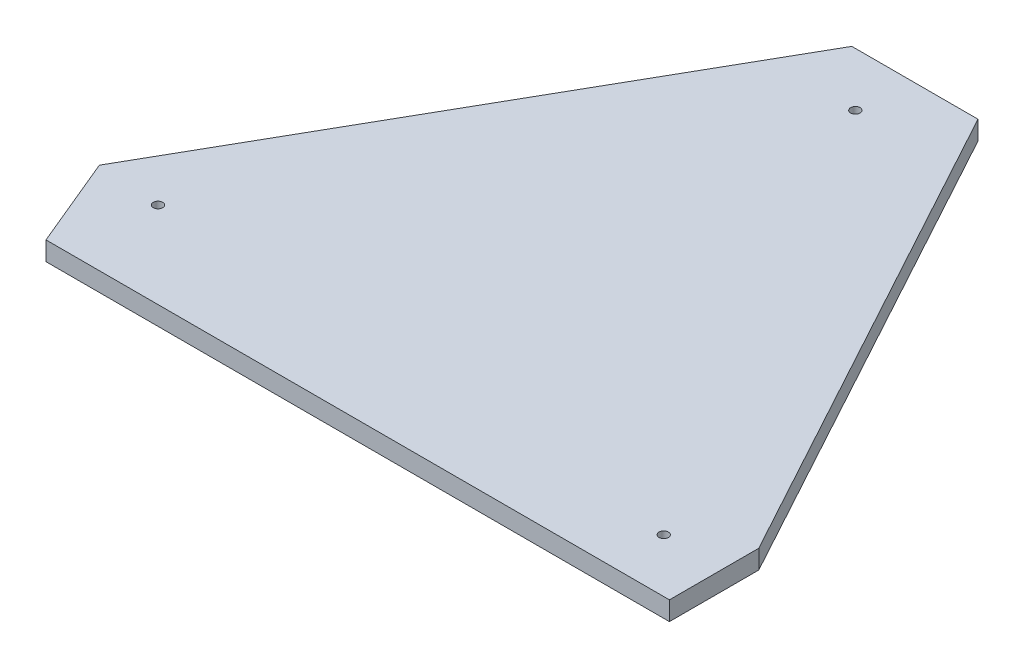
SolidWorks part; units mm, degrees
material "Cedar"
ref_plane "Front Plane" through (0, 0, 0) normal (0, 0, 1) x (1, 0, 0)
ref_plane "Top Plane" through (0, 0, 0) normal (0, 1, 0) x (1, 0, 0)
ref_plane "Right Plane" through (0, 0, 0) normal (1, 0, 0) x (0, 0, -1)
sketch "Sketch1" plane through (0, 0, 0) normal (0, 1, 0) x (1, 0, 0)
  line L0 (0, 0) -> (-523.875, 0)
  line L1 (-523.875, 0) -> (-555.8494, 76.7944)
  line L2 (-555.8494, 76.7944) -> (-326.1382, 479.425)
  line L3 (-326.1382, 479.425) -> (-220.1186, 479.425)
  line L4 (-220.1186, 479.425) -> (0, 75.0824)
  line L5 (0, 75.0824) -> (0, 0)
  point P5 (-523.875, 0)
  point P8 (-575.9866, 64.8392)
  point P9 (-571.7144, 75.0824)
  point P10 (-366.6877, 454.5522)
  dimension "D1" = 523.875
  dimension "D2" = 83.185
  dimension "D3" = 75.0824
  dimension "D4" = 460.375
  dimension "D5" = 106.0196
  dimension "D6" = 463.55
  dimension "D7" = 479.425
extrude "Boss-Extrude1" add sketch "Sketch1" along normal blind 15.875
sketch "Sketch2" plane through (0, 15.875, 0) normal (0, 1, 0) x (1, 0, 0)
  line L0 (-220.1186, 479.425) -> (-326.1382, 479.425) construction
  line L1 (-523.875, 0) -> (0, 0) construction
  line L2 (0, 0) -> (0, 75.0824) construction
  circle A0 centre (-278.1068, 434.34) radius 3.9688
  circle A1 centre (-502.2046, 72.4408) radius 3.9688
  circle A2 centre (-49.7332, 44.9326) radius 3.9687
  dimension "D1" = 7.9375
  dimension "D2" = 7.9375
  dimension "D3" = 7.9375
  dimension "D6" = 72.4408
  dimension "D8" = 44.9326
  dimension "D4" = 45.085
  dimension "D5" = 48.0314
  dimension "D7" = 53.6448
  dimension "D9" = 49.7332
extrude "Cut-Extrude1" cut sketch "Sketch2" against normal through all
